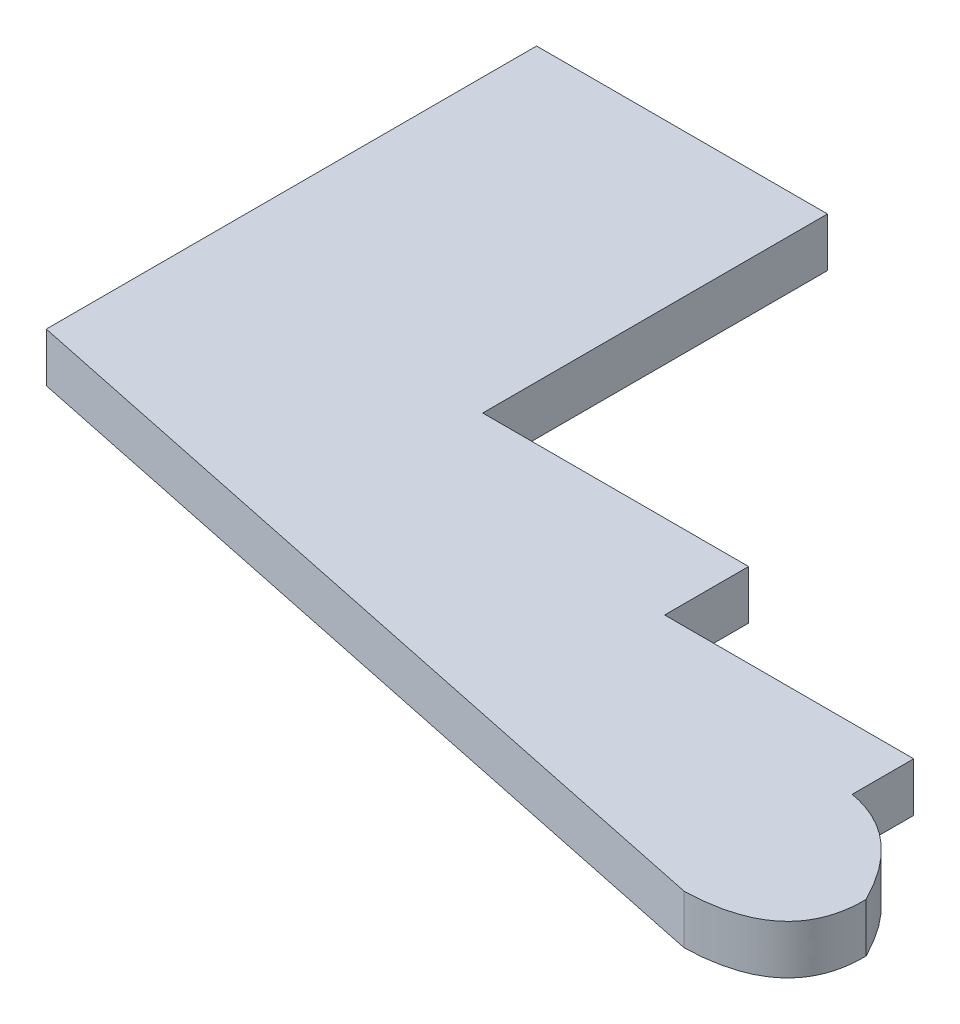
SolidWorks part; units mm, degrees
ref_plane "Front Plane" through (0, 0, 0) normal (0, 0, 1) x (1, 0, 0)
ref_plane "Top Plane" through (0, 0, 0) normal (0, 1, 0) x (1, 0, 0)
ref_plane "Right Plane" through (0, 0, 0) normal (1, 0, 0) x (0, 0, -1)
sketch "Sketch2" plane through (0, 0, 0) normal (0, 1, 0) x (1, 0, 0)
  line L0 (0, 0) -> (30.1307, 0)
  line L12 (30.1307, -29.6216) -> (30.1307, 0)
  line L13 (0, 0) -> (0, -50.7825)
  line L16 (0, -50.7825) -> (83.4676, -68.1749)
  line L17 (83.4676, -50.7825) -> (83.4676, -68.1749) construction
  line L18 (83.4676, -50.7825) -> (83.4676, -44.4052)
  line L19 (83.4676, -44.4052) -> (57.6688, -44.4052)
  line L20 (57.6688, -44.4052) -> (57.6688, -35.709)
  line L21 (57.6688, -35.709) -> (30.1307, -35.709)
  line L22 (30.1307, -35.709) -> (30.1307, -29.6216)
  spline S0 degree 2 poles (83.4676, -68.1749) (93.7466, -67.9086) (93.6132, -59.4787) knots 0 0 0 1 1 1
  spline S1 degree 2 poles (93.6132, -59.4787) (89.754, -51.85) (83.4676, -50.7825) knots 0 0 0 0.754492 0.754492 0.754492
extrude "Boss-Extrude2" add sketch "Sketch2" along normal blind 5.08
